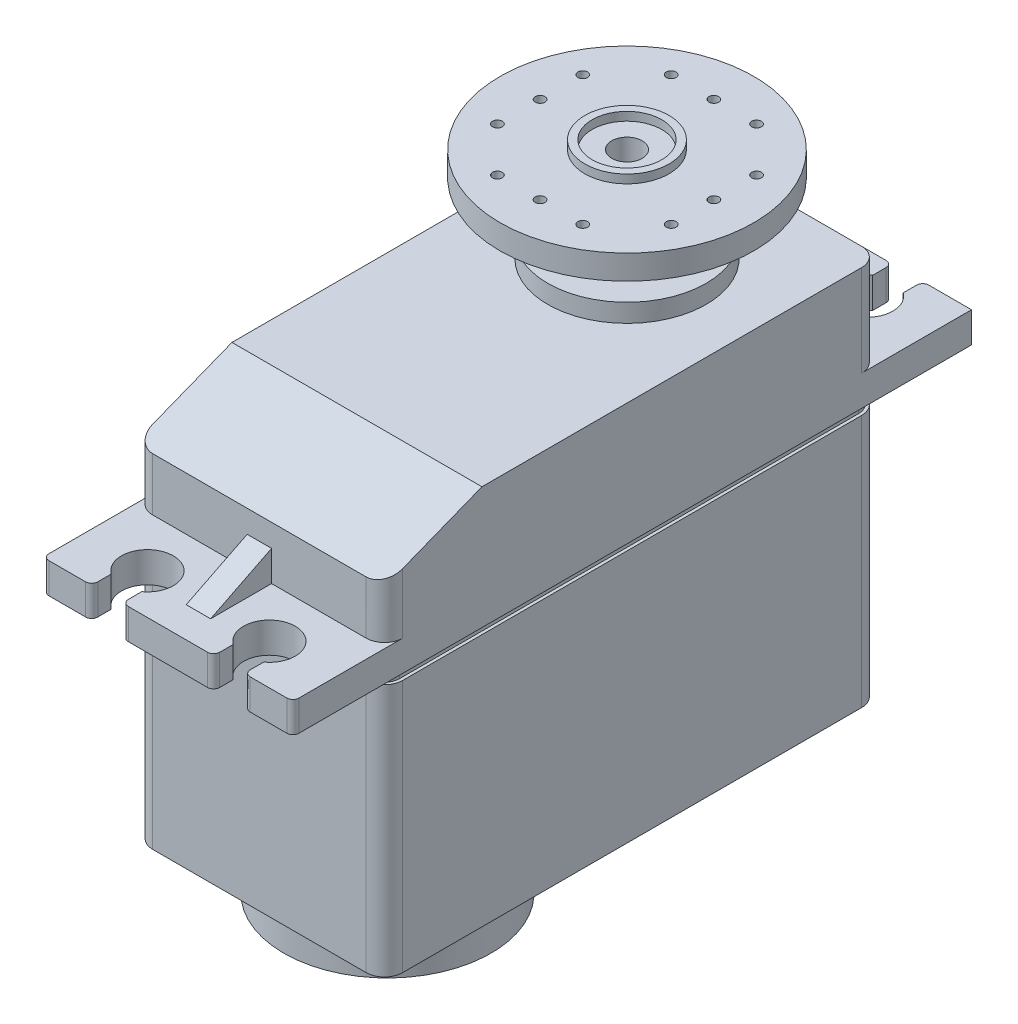
SolidWorks part; units mm, degrees
ref_plane "Front Plane" through (0, 0, 0) normal (0, 0, 1) x (1, 0, 0)
ref_plane "Top Plane" through (0, 0, 0) normal (0, 1, 0) x (1, 0, 0)
ref_plane "Right Plane" through (0, 0, 0) normal (1, 0, 0) x (0, 0, -1)
sketch "Sketch1" plane through (0, 0, 0) normal (0, 1, 0) x (1, 0, 0)
  line L1 (-10.25, 0) -> (10.25, 0)
  line L2 (-10.25, 0) -> (-10.25, 40.64)
  line L3 (-10.25, 40.64) -> (10.25, 40.64)
  line L4 (10.25, 0) -> (10.25, 40.64)
  dimension "D1" = 20.5
  dimension "D2" = 40.64
extrude "Boss-Extrude1" add sketch "Sketch1" along normal blind 39.5
sketch "Sketch2" plane through (10.25, 0, 0) normal (1, 0, 0) x (0, 0, -1)
  line L0 (0, 39.5) -> (0, 36.35)
  line L1 (0, 39.5) -> (0, 0) construction
  line L2 (0, 36.35) -> (8, 39.5)
  line L3 (0, 39.5) -> (40.64, 39.5) construction
  line L4 (8, 39.5) -> (0, 39.5)
  dimension "D1" = 8
  dimension "D2" = 3.15
extrude "Cut-Extrude1" cut sketch "Sketch2" against normal through all
sketch "Sketch3" plane through (10.25, 0, 0) normal (1, 0, 0) x (0, 0, -1)
  line L0 (0, 0) -> (40.64, 0) construction
  line L1 (-7.5, 32) -> (48.14, 32)
  line L2 (-7.5, 32) -> (-7.5, 29.5)
  line L3 (-7.5, 29.5) -> (48.14, 29.5)
  line L4 (48.14, 32) -> (48.14, 29.5)
  line L5 (20.32, 0) -> (20.32, 29.5) construction
  line L6 (40.64, 39.5) -> (40.64, 0) construction
  dimension "D1" = 29.5
  dimension "D2" = 2.5
  dimension "D3" = 7.5
extrude "Boss-Extrude2" add sketch "Sketch3" against normal up to surface (20.5 mm away) up to face at (-10.25, 23.07, -17.856)
sketch "Sketch4" plane through (0, 32, 0) normal (0, 1, 0) x (1, 0, 0)
  line L0 (0, -7.5) -> (0, 48.14) construction
  line L1 (-10.25, -7.5) -> (10.25, -7.5) construction
  line L2 (-10.25, 48.14) -> (10.25, 48.14) construction
  line L3 (0, 20.32) -> (-5.2177, 20.32) construction
  circle A0 centre (-5, -4.18) radius 2.125
  circle A1 centre (5, -4.18) radius 2.125
  circle A2 centre (5, 44.82) radius 2.125
  circle A3 centre (-5, 44.82) radius 2.125
  dimension "D3" = 4.25
  dimension "D1" = 10
  dimension "D2" = 49
extrude "Cut-Extrude2" cut sketch "Sketch4" against normal through all
sketch "Sketch5" plane through (0, 32, 0) normal (0, 1, 0) x (1, 0, 0)
  line L0 (0, -7.5) -> (0, 48.14) construction
  line L1 (-10.25, -7.5) -> (10.25, -7.5) construction
  line L2 (-10.25, 48.14) -> (10.25, 48.14) construction
  line L3 (0, 20.32) -> (-11.2232, 20.32) construction
  line L4 (-5, -4.18) -> (-5, -7.5) construction
  line L5 (3.75, -7.5) -> (6.25, -7.5)
  line L6 (-3.75, -7.5) -> (-6.25, -7.5)
  line L7 (-3.75, -7.5) -> (-3.75, -5.8985)
  line L8 (-3.75, -5.8985) -> (-6.25, -5.8985)
  line L9 (-6.25, -7.5) -> (-6.25, -5.8985)
  line L10 (3.75, -7.5) -> (3.75, -5.8985)
  line L11 (3.75, -5.8985) -> (6.25, -5.8985)
  line L12 (6.25, -7.5) -> (6.25, -5.8985)
  line L13 (-3.75, 48.14) -> (-6.25, 48.14)
  line L14 (-6.25, 48.14) -> (-6.25, 46.5385)
  line L15 (-3.75, 46.5385) -> (-6.25, 46.5385)
  line L16 (-3.75, 48.14) -> (-3.75, 46.5385)
  line L17 (3.75, 48.14) -> (6.25, 48.14)
  line L18 (6.25, 48.14) -> (6.25, 46.5385)
  line L19 (3.75, 46.5385) -> (6.25, 46.5385)
  line L20 (3.75, 48.14) -> (3.75, 46.5385)
  circle A0 centre (-5, -4.18) radius 2.125 construction
  dimension "D1" = 2.5
extrude "Cut-Extrude3" cut sketch "Sketch5" against normal through all
sketch "Sketch6" plane through (0, 0, 0) normal (1, 0, 0) x (0, 0, -1)
  line L0 (0, 36.35) -> (0, 32) construction
  line L1 (0, 36.35) -> (0, 32) construction
  line L2 (0, 32) -> (-5, 32)
  line L3 (-5, 32) -> (0, 34.5)
  line L4 (0, 34.5) -> (0, 32)
  line L5 (0, 0) -> (40.64, 0) construction
  line L6 (0, 0) -> (40.64, 0) construction
  line L7 (20.32, 0) -> (20.32, 45.2439) construction
  line L8 (40.64, 32) -> (45.64, 32)
  line L9 (40.64, 34.5) -> (40.64, 32)
  line L10 (45.64, 32) -> (40.64, 34.5)
  dimension "D1" = 5
  dimension "D2" = 2.5
extrude "Boss-Extrude3" add sketch "Sketch6" along normal mid plane 2
sketch "Sketch7" plane through (0, 39.5, 0) normal (0, 1, 0) x (1, 0, 0)
  line L0 (0, 40.64) -> (0, 8) construction
  line L1 (10.25, 40.64) -> (-10.25, 40.64) construction
  line L2 (-10.25, 8) -> (10.25, 8) construction
  circle A0 centre (0, 30.14) radius 6.5
  dimension "D1" = 13
  dimension "D2" = 10.5
extrude "Boss-Extrude4" add sketch "Sketch7" along normal blind 1.5
sketch "Sketch8" plane through (0, 41, 0) normal (0, 1, 0) x (1, 0, 0)
  circle A0 centre (0, 30.14) radius 2.9
  dimension "D1" = 5.8
extrude "Boss-Extrude5" add sketch "Sketch8" along normal blind 1.25
sketch "Sketch9" plane through (0, 42.25, 0) normal (0, 1, 0) x (1, 0, 0)
  circle A0 centre (0, 30.14) radius 4.445
  dimension "D1" = 8.89
extrude "Boss-Extrude6" add sketch "Sketch9" along normal offset from surface (3 mm away) 5.75 up to face at (0, 39.5, -24.32) offset beyond the face yes
sketch "Sketch10" plane through (0, 45.25, 0) normal (0, 1, 0) x (1, 0, 0)
  circle A0 centre (0, 30.14) radius 10.4
  dimension "D1" = 20.8
extrude "Boss-Extrude7" add sketch "Sketch10" along normal blind 2
sketch "Sketch11" plane through (0, 47.25, 0) normal (0, 1, 0) x (1, 0, 0)
  circle A0 centre (0, 30.14) radius 1.25
  dimension "D1" = 2.5
extrude "Cut-Extrude4" cut sketch "Sketch11" against normal up to surface (7.75 mm away) up to face at (0, 39.5, -24.32)
sketch "Sketch12" plane through (0, 47.25, 0) normal (0, 1, 0) x (1, 0, 0)
  circle A0 centre (0, 30.14) radius 3.45
  circle A1 centre (0, 30.14) radius 2.85
  dimension "D1" = 5.7
  dimension "D2" = 6.9
extrude "Boss-Extrude8" add sketch "Sketch12" along normal blind 0.7
sketch "Sketch13" plane through (0, 47.25, 0) normal (0, 1, 0) x (1, 0, 0)
  line L0 (0, 40.54) -> (0, 19.74) construction
  line L1 (0, 37.265) -> (3.5, 37.265) construction
  circle A0 centre (0, 30.14) radius 10.4 construction
  circle A1 centre (0, 37.265) radius 0.4
  circle A2 centre (0, 30.14) radius 1.25 construction
  circle A3 centre (3.5, 37.265) radius 0.4
  circle A4 centre (-3.5, 37.265) radius 0.4
  circle A5 centre (7.125, 26.64) radius 0.4
  circle A6 centre (7.125, 30.14) radius 0.4
  circle A7 centre (7.125, 33.64) radius 0.4
  circle A8 centre (-3.5, 23.015) radius 0.4
  circle A9 centre (0, 23.015) radius 0.4
  circle A10 centre (3.5, 23.015) radius 0.4
  circle A11 centre (-7.125, 33.64) radius 0.4
  circle A12 centre (-7.125, 30.14) radius 0.4
  circle A13 centre (-7.125, 26.64) radius 0.4
  point P13 (0, 30.14)
  point P35 (0, 30.14)
  dimension "D1" = 0.8
  dimension "D2" = 7.125
  dimension "D3" = 3.5
  dimension "D4" = 4
extrude "Cut-Extrude5" cut sketch "Sketch13" against normal up to surface (2 mm away) up to face at (0, 45.25, -19.74)
fillet "Fillet1" radius 1.5 8 edges at (10.25, 14.75, -40.64) (10.25, 35.75, -40.64) (-10.25, 14.75, -40.64) (-10.25, 35.75, -40.64) (10.25, 14.75, 0) (10.25, 34.175, 0) (-10.25, 34.175, 0) (-10.25, 14.75, 0)
fillet "Fillet2" radius 0.5 11 edges at (6.25, 30.75, -48.14) (3.75, 30.75, -48.14) (-3.75, 30.75, -48.14) (-6.25, 30.75, -48.14) (-10.25, 30.75, -48.14) (10.25, 30.75, 7.5) (6.25, 30.75, 7.5) (3.75, 30.75, 7.5) (-3.75, 30.75, 7.5) (-6.25, 30.75, 7.5) (-10.25, 30.75, 7.5)
sketch "Sketch14" plane through (0, 0, 0) normal (0, -1, 0) x (1, 0, 0)
  line L1 (8.75, -0.25) -> (-8.75, -0.25)
  line L2 (-10, -1.5) -> (-10, -39.14)
  line L3 (-8.75, -40.39) -> (8.75, -40.39)
  line L4 (10, -39.14) -> (10, -1.5)
  line L5 (-8.75, -40.64) -> (8.75, -40.64)
  line L6 (10.25, -39.14) -> (10.25, -1.5)
  line L7 (8.75, 0) -> (-8.75, 0)
  line L8 (-10.25, -1.5) -> (-10.25, -39.14)
  line L9 (-8.75, -40.64) -> (8.75, -40.64)
  line L10 (10.25, -39.14) -> (10.25, -1.5)
  line L11 (8.75, 0) -> (-8.75, 0)
  line L12 (-10.25, -1.5) -> (-10.25, -39.14)
  arc A0 (-8.75, -0.25) -> (-10, -1.5) centre (-8.75, -1.5) ccw
  arc A1 (-10, -39.14) -> (-8.75, -40.39) centre (-8.75, -39.14) ccw
  arc A2 (8.75, -40.39) -> (10, -39.14) centre (8.75, -39.14) ccw
  arc A3 (10, -1.5) -> (8.75, -0.25) centre (8.75, -1.5) ccw
  arc A4 (8.75, -40.64) -> (10.25, -39.14) centre (8.75, -39.14) ccw
  arc A5 (10.25, -1.5) -> (8.75, 0) centre (8.75, -1.5) ccw
  arc A6 (-8.75, 0) -> (-10.25, -1.5) centre (-8.75, -1.5) ccw
  arc A7 (-10.25, -39.14) -> (-8.75, -40.64) centre (-8.75, -39.14) ccw
  arc A8 (8.75, -40.64) -> (10.25, -39.14) centre (8.75, -39.14) ccw
  arc A9 (10.25, -1.5) -> (8.75, 0) centre (8.75, -1.5) ccw
  arc A10 (-8.75, 0) -> (-10.25, -1.5) centre (-8.75, -1.5) ccw
  arc A11 (-10.25, -39.14) -> (-8.75, -40.64) centre (-8.75, -39.14) ccw
  dimension "D1" = 0
  dimension "D2" = 0.25
extrude "Cut-Extrude6" cut sketch "Sketch14" against normal blind 0.5 from offset 7.75 offset against normal yes
sketch "Sketch15" plane through (0, 29.5, 0) normal (0, -1, 0) x (1, 0, 0)
  line L4 (-8.75, -40.64) -> (8.75, -40.64)
  line L5 (10.25, -39.14) -> (10.25, -1.5)
  line L6 (8.75, 0) -> (-8.75, 0)
  line L7 (-10.25, -1.5) -> (-10.25, -39.14)
  line L8 (-8.75, -40.64) -> (8.75, -40.64)
  line L9 (10.25, -39.14) -> (10.25, -1.5)
  line L10 (8.75, 0) -> (-8.75, 0)
  line L11 (-10.25, -1.5) -> (-10.25, -39.14)
  line L13 (10, -39.14) -> (10, -1.5)
  line L14 (-8.75, -40.39) -> (8.75, -40.39)
  line L15 (-10, -1.5) -> (-10, -39.14)
  line L16 (8.75, -0.25) -> (-8.75, -0.25)
  line L17 (10, -39.14) -> (10, -1.5)
  line L18 (-8.75, -40.39) -> (8.75, -40.39)
  line L19 (-10, -1.5) -> (-10, -39.14)
  line L20 (8.75, -0.25) -> (-8.75, -0.25)
  arc A4 (-10.25, -39.14) -> (-8.75, -40.64) centre (-8.75, -39.14) ccw
  arc A5 (8.75, -40.64) -> (10.25, -39.14) centre (8.75, -39.14) ccw
  arc A6 (10.25, -1.5) -> (8.75, 0) centre (8.75, -1.5) ccw
  arc A7 (-8.75, 0) -> (-10.25, -1.5) centre (-8.75, -1.5) ccw
  arc A8 (-10.25, -39.14) -> (-8.75, -40.64) centre (-8.75, -39.14) ccw
  arc A9 (8.75, -40.64) -> (10.25, -39.14) centre (8.75, -39.14) ccw
  arc A10 (10.25, -1.5) -> (8.75, 0) centre (8.75, -1.5) ccw
  arc A11 (-8.75, 0) -> (-10.25, -1.5) centre (-8.75, -1.5) ccw
  arc A12 (8.75, -40.39) -> (10, -39.14) centre (8.75, -39.14) ccw
  arc A13 (-10, -39.14) -> (-8.75, -40.39) centre (-8.75, -39.14) ccw
  arc A14 (-8.75, -0.25) -> (-10, -1.5) centre (-8.75, -1.5) ccw
  arc A15 (10, -1.5) -> (8.75, -0.25) centre (8.75, -1.5) ccw
  arc A16 (8.75, -40.39) -> (10, -39.14) centre (8.75, -39.14) ccw
  arc A17 (-10, -39.14) -> (-8.75, -40.39) centre (-8.75, -39.14) ccw
  arc A18 (-8.75, -0.25) -> (-10, -1.5) centre (-8.75, -1.5) ccw
  arc A19 (10, -1.5) -> (8.75, -0.25) centre (8.75, -1.5) ccw
  dimension "D1" = 0
  dimension "D2" = 0
extrude "Cut-Extrude7" cut sketch "Sketch15" along normal blind 0.5
sketch "Sketch16" plane through (10.25, 0, 0) normal (1, 0, 0) x (0, 0, -1)
  line L0 (39.14, 8.25) -> (1.5, 8.25) construction
  line L2 (39.14, 8.25) -> (1.5, 8.25) construction
  line L5 (0, 0) -> (50.4396, 0)
  line L6 (0, 0) -> (0, 8.25)
  line L7 (0, 8.25) -> (50.4396, 8.25)
  line L8 (50.4396, 0) -> (50.4396, 8.25)
extrude "Cut-Extrude8" cut sketch "Sketch16" against normal through all
sketch "Sketch17" plane through (0, 8.25, 0) normal (0, -1, 0) x (1, 0, 0)
  line L0 (0, 0) -> (0, -40.64) construction
  line L1 (8.75, 0) -> (-8.75, 0) construction
  line L2 (-8.75, -40.64) -> (8.75, -40.64) construction
  circle A0 centre (0, -10.5) radius 8.5
  point P8 (0, -2)
  dimension "D1" = 17
  dimension "D2" = 2
extrude "Boss-Extrude9" add sketch "Sketch17" along normal blind 4
